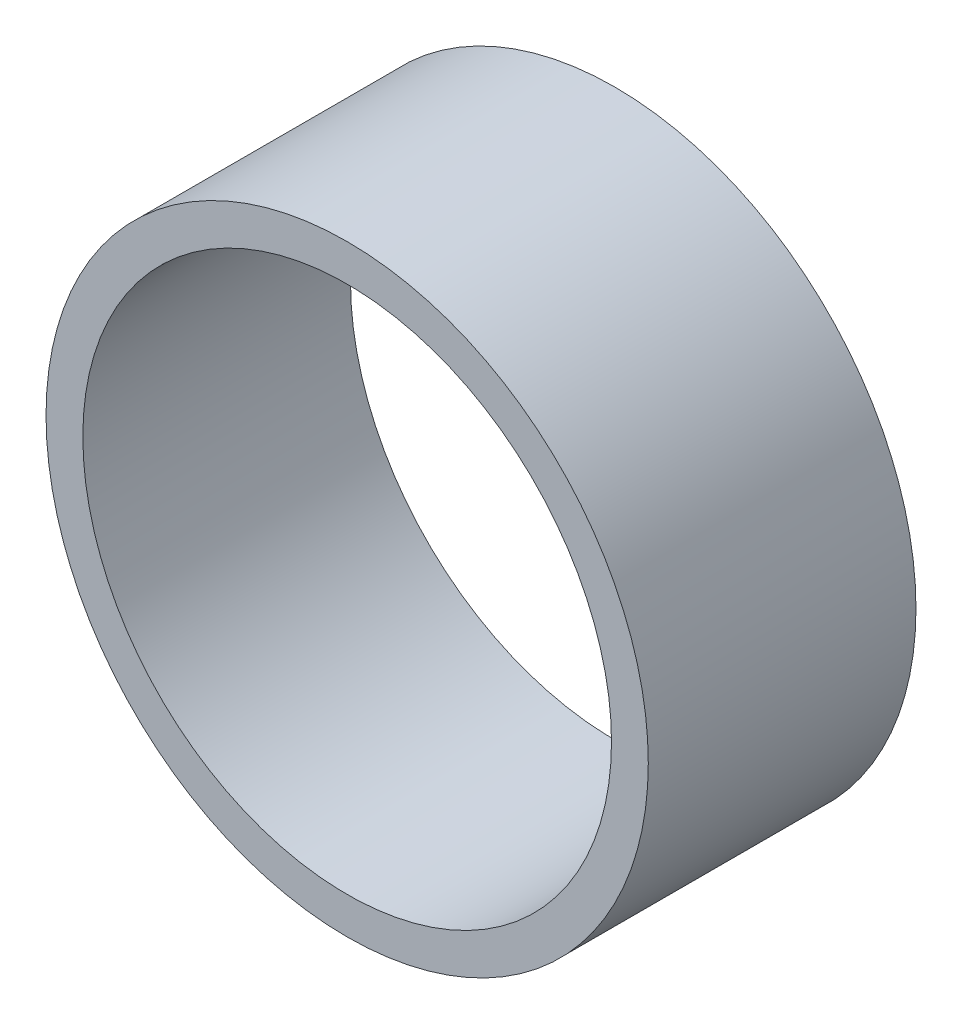
SolidWorks part; units mm, degrees
ref_plane "Front Plane" through (0, 0, 0) normal (0, 0, 1) x (1, 0, 0)
ref_plane "Top Plane" through (0, 0, 0) normal (0, 1, 0) x (1, 0, 0)
ref_plane "Right Plane" through (0, 0, 0) normal (1, 0, 0) x (0, 0, -1)
sketch "Sketch1" plane through (0, 0, 0) normal (0, 0, 1) x (1, 0, 0)
  circle A0 centre (0, 0) radius 25.0825
  circle A1 centre (0, 0) radius 28.575
  dimension "D1" = 50.165
  dimension "D2" = 57.15
extrude "Boss-Extrude1" add sketch "Sketch1" along normal blind 25.4
